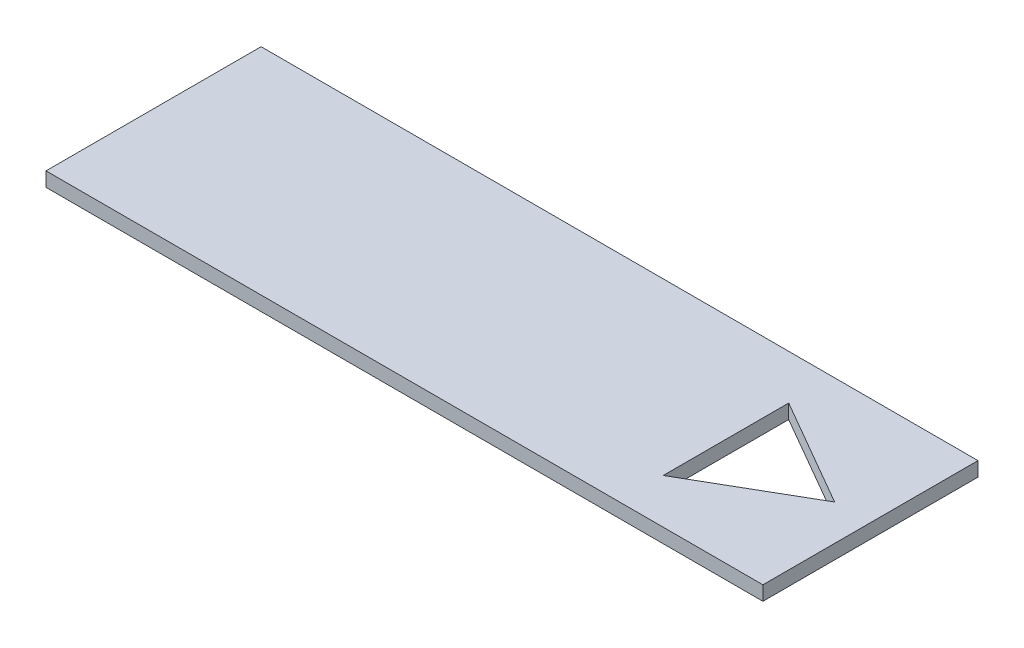
SolidWorks part; units mm, degrees
ref_plane "Front Plane" through (0, 0, 0) normal (0, 0, 1) x (1, 0, 0)
ref_plane "Top Plane" through (0, 0, 0) normal (0, 1, 0) x (1, 0, 0)
ref_plane "Right Plane" through (0, 0, 0) normal (1, 0, 0) x (0, 0, -1)
sketch "Sketch1" plane through (0, 0, 0) normal (0, 1, 0) x (1, 0, 0)
  line L1 (0, 0) -> (200, 0)
  line L2 (0, 0) -> (0, 60)
  line L3 (0, 60) -> (200, 60)
  line L4 (200, 0) -> (200, 60)
  dimension "D1" = 200
  dimension "D2" = 60
extrude "Boss-Extrude1" add sketch "Sketch1" along normal blind 4
sketch "Sketch2" plane through (0, 4, 0) normal (0, 1, 0) x (1, 0, 0)
  line L0 (190, 30) -> (159.6891, 47.5)
  line L1 (159.6891, 47.5) -> (159.6891, 12.5)
  line L2 (159.6891, 12.5) -> (190, 30)
  line L3 (200, 30) -> (190, 30) construction
  line L4 (200, 0) -> (200, 60) construction
  point P4 (152.9921, 12.5)
  dimension "D1" = 35
  dimension "D2" = 10
extrude "Cut-Extrude1" cut sketch "Sketch2" against normal through all
